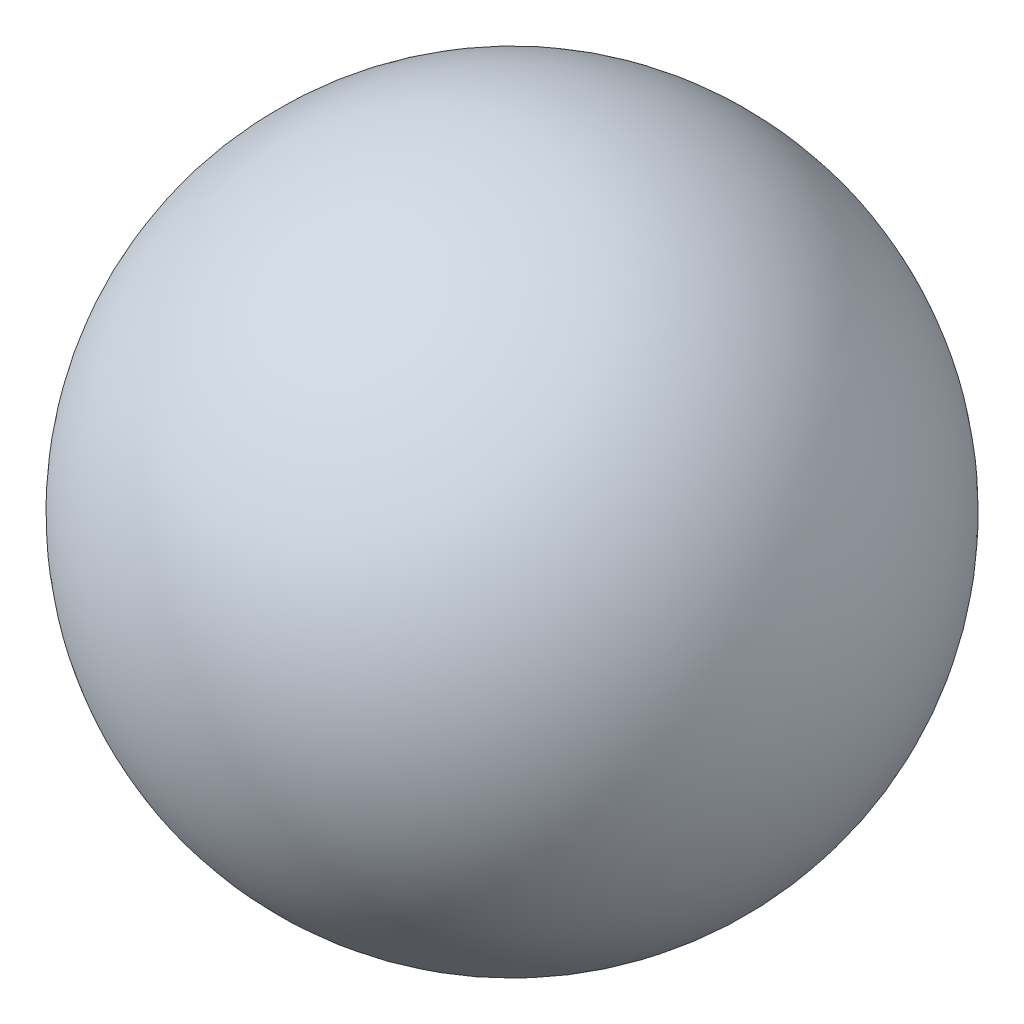
SolidWorks part; units mm, degrees
ref_plane "Front Plane" through (0, 0, 0) normal (0, 0, 1) x (1, 0, 0)
ref_plane "Top Plane" through (0, 0, 0) normal (0, 1, 0) x (1, 0, 0)
ref_plane "Right Plane" through (0, 0, 0) normal (1, 0, 0) x (0, 0, -1)
sketch "Sketch1" plane through (0, 0, 0) normal (0, 1, 0) x (1, 0, 0)
  line L0 (0, -0.05) -> (0, 0.05)
  arc A1 (0, 0.05) -> (0, -0.05) centre (0, 0) cw
revolve "Revolve1" add sketch "Sketch1" angle 360 about L0
